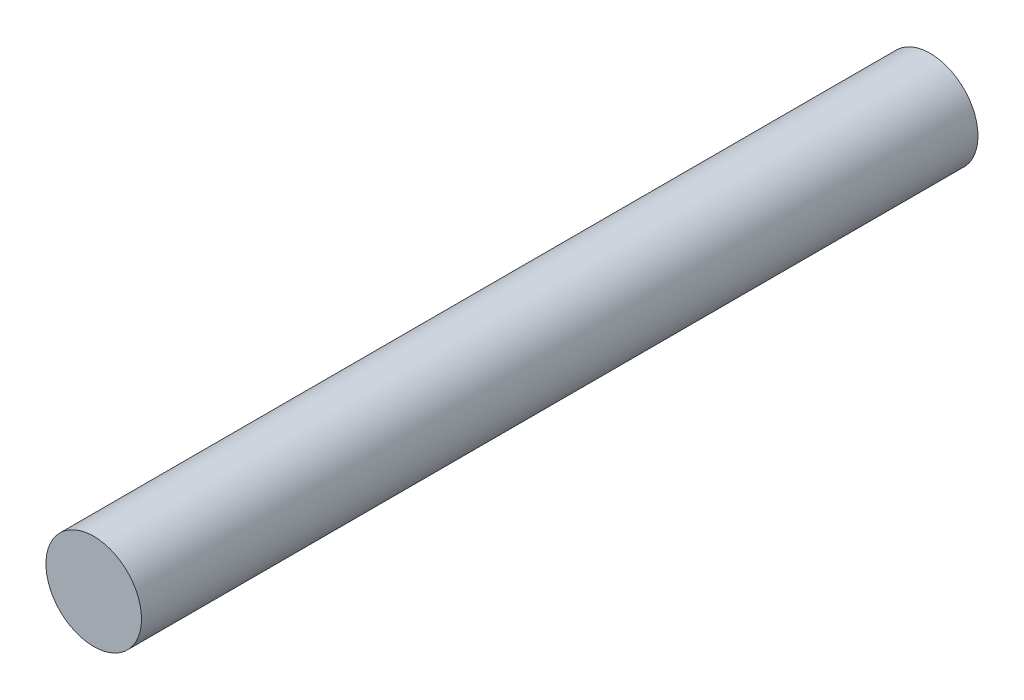
SolidWorks part; units mm, degrees
ref_plane "Plan de face" through (0, 0, 0) normal (0, 0, 1) x (1, 0, 0)
ref_plane "Plan de dessus" through (0, 0, 0) normal (0, 1, 0) x (1, 0, 0)
ref_plane "Plan de droite" through (0, 0, 0) normal (1, 0, 0) x (0, 0, -1)
sketch "Esquisse1" plane through (0, 0, 0) normal (0, 0, 1) x (1, 0, 0)
  circle A0 centre (280, 0) radius 4 construction
  circle A1 centre (280, 0) radius 4
extrude "Boss.-Extru.1" add sketch "Esquisse1" along normal blind 70
